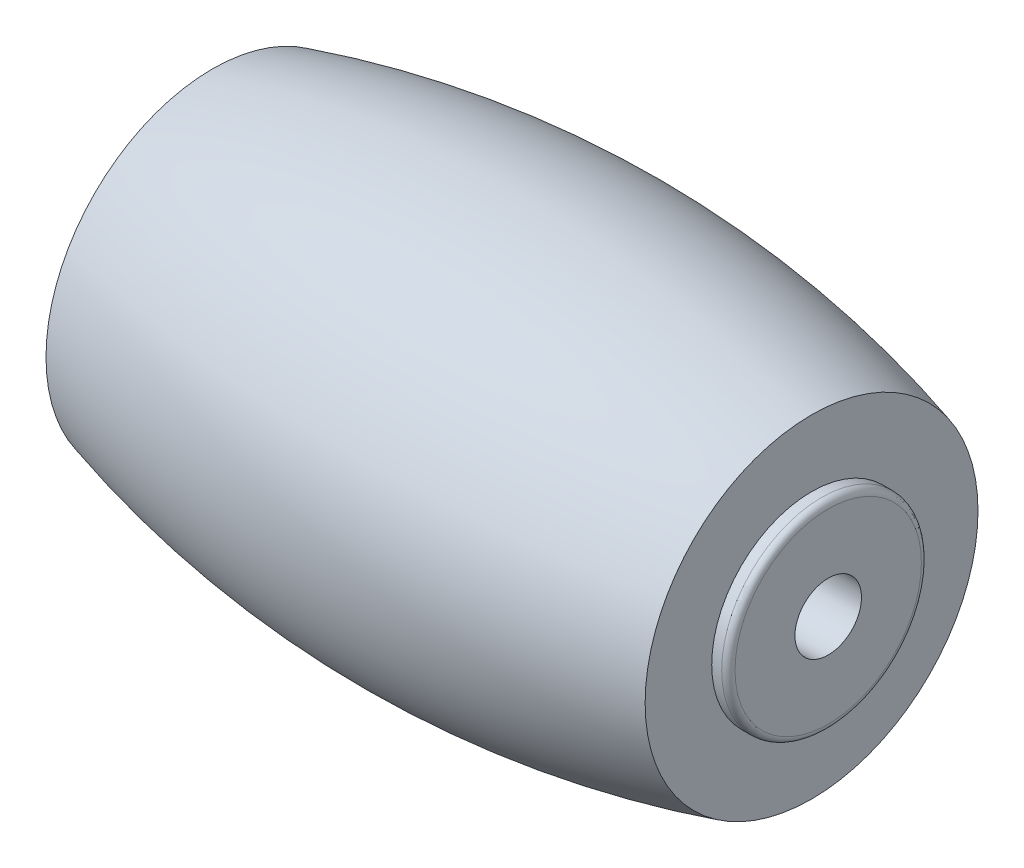
SolidWorks part; units mm, degrees
ref_plane "Front Plane" through (0, 0, 0) normal (0, 0, 1) x (1, 0, 0)
ref_plane "Top Plane" through (0, 0, 0) normal (0, 1, 0) x (1, 0, 0)
ref_plane "Right Plane" through (0, 0, 0) normal (1, 0, 0) x (0, 0, -1)
sketch "Sketch1" plane through (0, 0, 0) normal (0, 1, 0) x (1, 0, 0)
  line L0 (0, 0) -> (-202751.7478, 0) construction
  line L1 (0, 0) -> (0, -202751.7478) construction
  line L2 (0, 0) -> (-9, 0)
  line L3 (-9, 0) -> (-9, 5)
  line L4 (0, 0) -> (9, 0)
  line L5 (9, 0) -> (9, 5)
  arc A0 (-9, 5) -> (9, 5) centre (0, -26.7836) cw
  dimension "D1" = 9
  dimension "D2" = 5
revolve "Revolve1" add sketch "Sketch1" angle 360 about L0
sketch "Sketch3" plane through (9, 0, 0) normal (1, 0, 0) x (0, 0, -1)
  circle A0 centre (0, 0) radius 3
  dimension "D1" = 6
extrude "Boss-Extrude1" add sketch "Sketch3" along normal blind 0.5
ref_plane "Plane1" through (0, 0, 0) normal (1, 0, 0) x (0, 0, -1)
mirror "Mirror1" about plane through (0, 0, 0) normal (1, 0, 0) of "Boss-Extrude1"
sketch "Sketch4" plane through (-9.5, 0, 0) normal (-1, 0, 0) x (0, 0, 1)
  circle A0 centre (0, 0) radius 1
  dimension "D1" = 2
extrude "Cut-Extrude2" cut sketch "Sketch4" against normal through all
fillet "Fillet1" radius 0.2 2 edges at (9.5, 0, -3) (-9.5, 0, -3)
